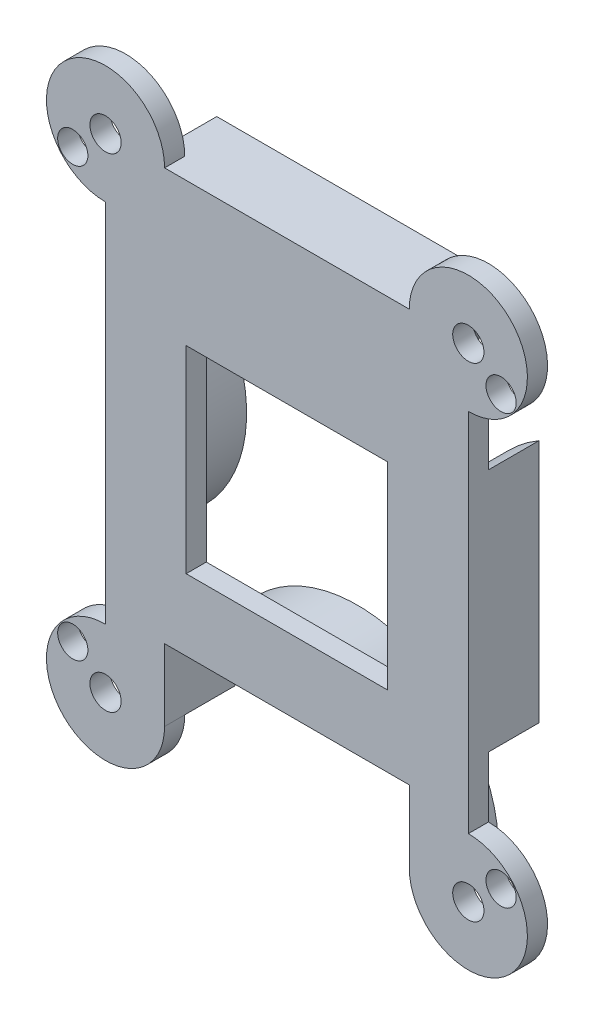
SolidWorks part; units mm, degrees
ref_plane "前视基准面" through (0, 0, 0) normal (0, 0, 1) x (1, 0, 0)
ref_plane "上视基准面" through (0, 0, 0) normal (0, 1, 0) x (1, 0, 0)
ref_plane "右视基准面" through (0, 0, 0) normal (1, 0, 0) x (0, 0, -1)
sketch "草图1" plane through (0, 0, 0) normal (0, 0, 1) x (1, 0, 0)
  line L0 (0, -55) -> (0, 55) construction
  line L1 (-18, 24) -> (18, 24)
  line L2 (-18, 24) -> (-18, -24)
  line L3 (-18, -24) -> (18, -24)
  line L4 (18, 24) -> (18, -24)
  line L5 (-18, 24) -> (18, -24) construction
  line L6 (-18, -24) -> (18, 24) construction
  line L7 (55, 0) -> (-55, 0) construction
  circle A0 centre (-25, 0) radius 14
  circle A1 centre (25, 0) radius 14
  circle A2 centre (0, 25) radius 14
  circle A3 centre (0, -25) radius 14
  point P0 (0, 0)
  dimension "D3" = 28
  dimension "D4" = 25
  dimension "D5" = 0
  dimension "D6" = 28
  dimension "D7" = 25
  dimension "D1" = 36
  dimension "D2" = 48
extrude "凸台-拉伸1" add sketch "草图1" against normal blind 5 contours L1 A2 | A1 L4 | L2 A0 | A3 L3
sketch "草图2" plane through (0, 0, 0) normal (0, 0, 1) x (1, 0, 0)
  line L0 (55, 0) -> (-55, 0) construction
  line L1 (-18, 24) -> (18, 24)
  line L2 (-18, 24) -> (-18, -24)
  line L3 (-18, -24) -> (18, -24)
  line L4 (18, 24) -> (18, -24)
  line L5 (-18, 24) -> (18, -24) construction
  line L6 (-18, -24) -> (18, 24) construction
  line L7 (0, -55) -> (0, 55) construction
  circle A0 centre (-18, 24) radius 1.55
  circle A1 centre (-18, -24) radius 1.55
  circle A2 centre (18, -24) radius 1.55
  circle A3 centre (18, 24) radius 1.55
  circle A4 centre (-18, 24) radius 5.8606
  circle A5 centre (-18, -24) radius 5.8606
  circle A6 centre (18, -24) radius 5.8606
  circle A7 centre (18, 24) radius 5.8606
  point P0 (0, 0)
  line M5 (-18, 12.1244) -> (-18, -12.1244)
  arc M6 (-18, -12.1244) -> (-18, 12.1244) centre (-25, 0) ccw
  dimension "D3" = 3.1
  dimension "D1" = 36
  dimension "D2" = 48
extrude "凸台-拉伸3" add sketch "草图2" along normal blind 2 contours L1 A4 L2 A0 | L2 A4 L1 A0 | L4 A7 L1 A4 L2 A5 L3 A6 M6 | M6 M5 | A7 L1 A3 L4 | A7 L4 A3 L1 | A5 L3 A1 L2 | L3 A6 L4 A2 | L4 A6 L3 A2 | A5 L2 A1 L3
sketch "草图3" plane through (0, 0, 0) normal (0, 0, -1) x (-1, 0, 0)
  line L1 (-10, 9.8022) -> (10, 9.8022)
  line L2 (-10, 9.8022) -> (-10, -9.8022)
  line L3 (-10, -9.8022) -> (10, -9.8022)
  line L4 (10, 9.8022) -> (10, -9.8022)
  line L5 (-10, 9.8022) -> (10, -9.8022) construction
  line L6 (-10, -9.8022) -> (10, 9.8022) construction
  point P0 (0, 0)
  dimension "D1" = 20
  dimension "D2" = 20
extrude "切除-拉伸1" cut sketch "草图3" against normal blind 2
sketch "草图4" plane through (0, 0, -5) normal (0, 0, -1) x (-1, 0, 0)
  line L0 (55, 0) -> (-55, 0) construction
  line L1 (0, 55) -> (0, -55) construction
  circle A0 centre (21.25, -21.25) radius 1.5
  circle A3 centre (21.25, 21.25) radius 1.5
  circle A4 centre (-21.25, 21.25) radius 1.5
  circle A5 centre (-21.25, -21.25) radius 1.5
  dimension "D1" = 3
  dimension "D3" = 21.25
  dimension "D2" = 21.25
extrude "切除-拉伸2" cut sketch "草图4" against normal blind 12
sketch "草图6" plane through (0, 0, 2) normal (0, 0, 1) x (1, 0, 0)
  line L0 (-12.1394, -24) -> (12.1394, -24) construction
  line L1 (12.1394, -16.8812) -> (-12.1394, -16.8812)
  line L2 (12.1394, -16.8812) -> (12.1394, -31.1188)
  line L3 (12.1394, -31.1188) -> (-12.1394, -31.1188)
  line L4 (-12.1394, -16.8812) -> (-12.1394, -31.1188)
  line L5 (12.1394, -16.8812) -> (-12.1394, -31.1188) construction
  line L6 (12.1394, -31.1188) -> (-12.1394, -16.8812) construction
  point P0 (0, -24)
extrude "切除-拉伸5" cut sketch "草图6" against normal blind 10
